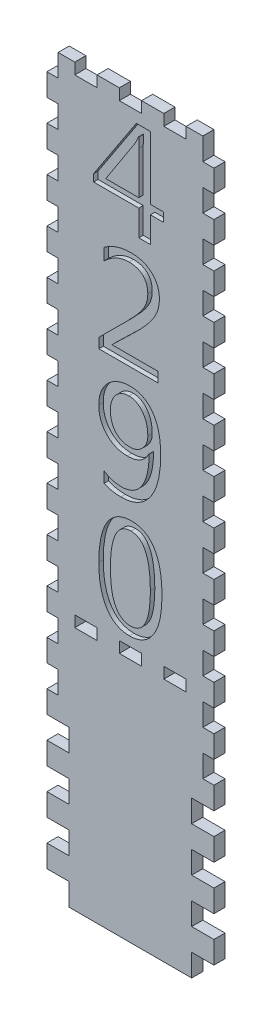
SolidWorks part; units mm, degrees
material "Pine"
ref_plane "Front Plane" through (0, 0, 0) normal (0, 0, 1) x (1, 0, 0)
ref_plane "Top Plane" through (0, 0, 0) normal (0, 1, 0) x (1, 0, 0)
ref_plane "Right Plane" through (0, 0, 0) normal (1, 0, 0) x (0, 0, -1)
sketch "Sketch2" plane through (0, 0, 0) normal (0, 0, 1) x (1, 0, 0)
  line L1 (0, 0) -> (95.25, 0)
  line L2 (0, 0) -> (0, 419.1)
  line L3 (0, 419.1) -> (95.25, 419.1)
  line L4 (95.25, 0) -> (95.25, 419.1)
  dimension "D1" = 95.25
  dimension "D2" = 419.1
extrude "Boss-Extrude1" add sketch "Sketch2" along normal blind 6.35
sketch "Sketch3" plane through (0, 0, 6.35) normal (0, 0, 1) x (1, 0, 0)
  line L1 (0, 0) -> (6.35, 0)
  line L2 (0, 0) -> (0, 12.7)
  line L3 (0, 12.7) -> (6.35, 12.7)
  line L4 (6.35, 0) -> (6.35, 12.7)
  line L5 (95.25, 0) -> (88.9, 0)
  line L6 (95.25, 0) -> (95.25, 12.7)
  line L7 (95.25, 12.7) -> (88.9, 12.7)
  line L8 (88.9, 0) -> (88.9, 12.7)
  dimension "D1" = 6.35
  dimension "D2" = 12.7
extrude "Cut-Extrude1" cut sketch "Sketch3" against normal through all
pattern_linear "LPattern1" count 17 spacing 25.4 along (0, 1, 0) of "Cut-Extrude1"
sketch "Sketch4" plane through (0, 0, 6.35) normal (0, 0, 1) x (1, 0, 0)
  line L0 (88.9, 419.1) -> (6.35, 419.1) construction
  line L1 (41.275, 419.1) -> (53.975, 419.1)
  line L2 (41.275, 419.1) -> (41.275, 412.75)
  line L3 (41.275, 412.75) -> (53.975, 412.75)
  line L4 (53.975, 419.1) -> (53.975, 412.75)
  line L5 (28.575, 419.1) -> (15.875, 419.1)
  line L6 (66.675, 419.1) -> (79.375, 419.1)
  line L7 (66.675, 419.1) -> (66.675, 412.75)
  line L8 (66.675, 412.75) -> (79.375, 412.75)
  line L9 (79.375, 419.1) -> (79.375, 412.75)
  line L10 (28.575, 419.1) -> (28.575, 412.75)
  line L11 (28.575, 412.75) -> (15.875, 412.75)
  line L12 (15.875, 419.1) -> (15.875, 412.75)
  point P14 (47.625, 419.1)
  dimension "D1" = 12.7
  dimension "D2" = 6.35
  dimension "D3" = 12.7
  dimension "D4" = 12.7
extrude "Cut-Extrude2" cut sketch "Sketch4" against normal through all
sketch "Sketch5" plane through (0, 0, 6.35) normal (0, 0, 1) x (1, 0, 0)
  line L0 (6.35, 0) -> (88.9, 0) construction
  line L1 (6.35, 12.7) -> (12.7, 12.7)
  line L2 (6.35, 12.7) -> (6.35, 0)
  line L3 (6.35, 0) -> (12.7, 0)
  line L4 (12.7, 12.7) -> (12.7, 0)
  line L5 (6.35, 12.7) -> (0, 12.7) construction
  line L6 (88.9, 12.7) -> (82.55, 12.7)
  line L7 (88.9, 12.7) -> (88.9, 0)
  line L8 (88.9, 0) -> (82.55, 0)
  line L9 (82.55, 12.7) -> (82.55, 0)
extrude "Cut-Extrude3" cut sketch "Sketch5" against normal through all
pattern_linear "LPattern2" count 4 spacing 25.4 along (0, 1, 0) of "Cut-Extrude3"
sketch "Sketch6" plane through (0, 0, 6.35) normal (0, 0, 1) x (1, 0, 0)
  line L0 (6.35, 139.7) -> (0, 139.7) construction
  line L1 (53.975, 139.7) -> (41.275, 139.7)
  line L2 (53.975, 139.7) -> (53.975, 146.05)
  line L3 (53.975, 146.05) -> (41.275, 146.05)
  line L4 (41.275, 139.7) -> (41.275, 146.05)
  line L5 (47.625, 139.7) -> (47.625, 0) construction
  line L6 (12.7, 0) -> (82.55, 0) construction
  dimension "D1" = 12.7
  dimension "D2" = 6.35
extrude "Cut-Extrude4" cut sketch "Sketch6" against normal through all
pattern_linear "LPattern3" count 2 spacing 25.4 along (1, 0, 0) count 2 spacing 25.4 along (-1, 0, 0) of "Cut-Extrude4"
sketch "Sketch7" plane through (0, 0, 6.35) normal (0, 0, 1) x (1, 0, 0)
  line L0 (25.908, 350.52) -> (25.908, -48.5983) construction
  text T0 "<r90>4290</r>" font "Segoe UI" height 55.88
  dimension "D1" = 25.908
  dimension "D2" = 350.52
extrude "Cut-Extrude5" cut sketch "Sketch7" against normal blind 2.54
